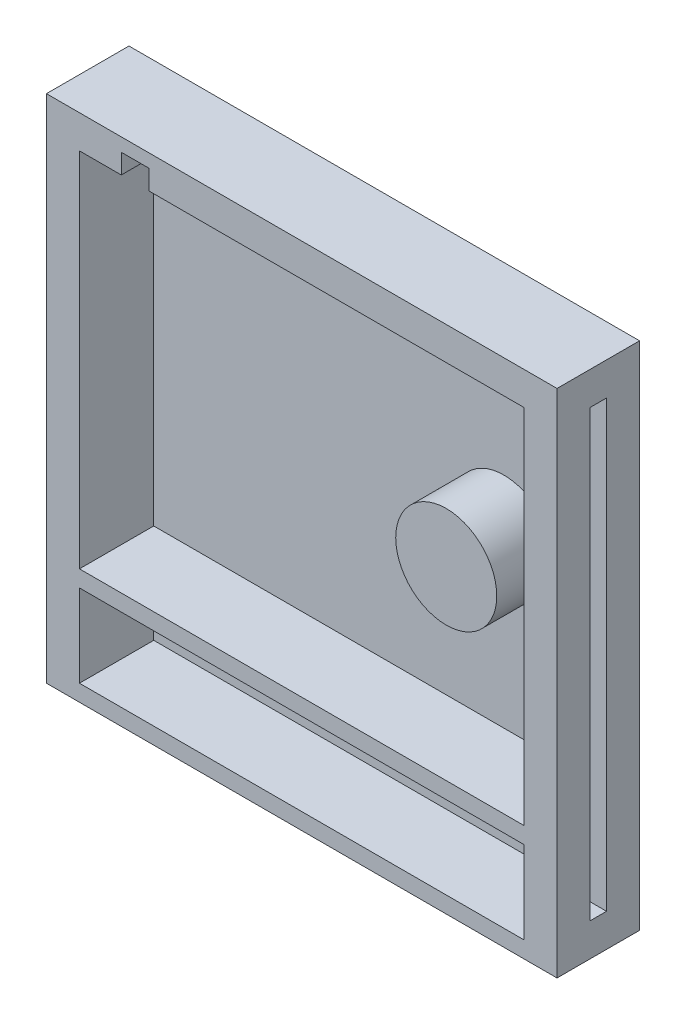
SolidWorks part; units mm, degrees
ref_plane "Front Plane" through (0, 0, 0) normal (0, 0, 1) x (1, 0, 0)
ref_plane "Top Plane" through (0, 0, 0) normal (0, 1, 0) x (1, 0, 0)
ref_plane "Right Plane" through (0, 0, 0) normal (1, 0, 0) x (0, 0, -1)
sketch "Sketch1" plane through (0, 0, 0) normal (0, 0, 1) x (1, 0, 0)
  line L1 (78.5679, 78.5679) -> (-78.5679, 78.5679)
  line L2 (78.5679, 78.5679) -> (78.5679, -78.5679)
  line L3 (78.5679, -78.5679) -> (-78.5679, -78.5679)
  line L4 (-78.5679, 78.5679) -> (-78.5679, -78.5679)
  line L5 (78.5679, 78.5679) -> (-78.5679, -78.5679) construction
  line L6 (78.5679, -78.5679) -> (-78.5679, 78.5679) construction
  point P0 (0, 0)
extrude "Boss-Extrude1" add sketch "Sketch1" along normal blind 25.4
sketch "Sketch2" plane through (0, 0, 25.4) normal (0, 0, 1) x (1, 0, 0)
  line L0 (78.5679, -78.5679) -> (78.5679, 78.5679) construction
  line L1 (68.4079, 68.4079) -> (-68.4079, 68.4079)
  line L2 (68.4079, 68.4079) -> (68.4079, -68.4079)
  line L3 (68.4079, -68.4079) -> (-68.4079, -68.4079)
  line L4 (-68.4079, 68.4079) -> (-68.4079, -68.4079)
  line L5 (68.4079, 68.4079) -> (-68.4079, -68.4079) construction
  line L6 (68.4079, -68.4079) -> (-68.4079, 68.4079) construction
  line L7 (-68.4079, -43.0079) -> (68.4079, -43.0079)
  point P0 (0, 0)
  dimension "D1" = 10.16
  dimension "D2" = 25.4
extrude "Cut-Extrude1" cut sketch "Sketch2" against normal offset from surface (22.86 mm away) 2.54 contours L4 L7 L2 L1 up to face at (0, 0, 0)
sketch "Sketch3" plane through (0, 0, 25.4) normal (0, 0, 1) x (1, 0, 0)
  line L0 (-68.4079, 68.4079) -> (-68.4079, -43.0079) construction
  line L1 (68.4079, -48.0879) -> (-68.4079, -48.0879)
  line L2 (68.4079, -48.0879) -> (68.4079, -73.4879)
  line L3 (68.4079, -73.4879) -> (-68.4079, -73.4879)
  line L4 (-68.4079, -48.0879) -> (-68.4079, -73.4879)
  line L5 (68.4079, 68.4079) -> (68.4079, -43.0079) construction
  line L6 (0, -48.0879) -> (0, -43.0079) construction
  line L7 (-68.4079, -43.0079) -> (68.4079, -43.0079) construction
  line L8 (0, -73.4879) -> (0, -78.5679) construction
  line L9 (-78.5679, -78.5679) -> (78.5679, -78.5679) construction
  dimension "D1" = 5.08
extrude "Cut-Extrude2" cut sketch "Sketch3" against normal offset from surface (22.86 mm away) 2.54 up to face at (0, 0, 0)
sketch "Sketch5" plane through (-78.5679, 0, 0) normal (-1, 0, 0) x (0, 0, 1)
  line L0 (15.24, 0) -> (25.4, 0) construction
  line L1 (15.24, -68.4079) -> (10.16, -68.4079)
  line L2 (15.24, -68.4079) -> (15.24, 68.4079)
  line L3 (15.24, 68.4079) -> (10.16, 68.4079)
  line L4 (10.16, -68.4079) -> (10.16, 68.4079)
  line L5 (25.4, 78.5679) -> (25.4, -78.5679) construction
  line L6 (10.16, 0) -> (0, 0) construction
  line L7 (0, 78.5679) -> (0, -78.5679) construction
  line L8 (25.4, 78.5679) -> (0, 78.5679) construction
  dimension "D1" = 5.08
  dimension "D2" = 10.16
extrude "Cut-Extrude3" cut sketch "Sketch5" against normal blind 7.62
mirror "Mirror1" about plane through (0, 0, 0) normal (1, 0, 0) of "Cut-Extrude3"
sketch "Sketch6" plane through (0, 0, 25.4) normal (0, 0, 1) x (1, 0, 0)
  line L0 (68.4079, 68.4079) -> (-68.4079, 68.4079) construction
  line L1 (-55.5371, 74.4708) -> (-47.0508, 74.4708)
  line L2 (-55.5371, 74.4708) -> (-55.5371, 68.4079)
  line L3 (-55.5371, 68.4079) -> (-47.0508, 68.4079)
  line L4 (-47.0508, 74.4708) -> (-47.0508, 68.4079)
extrude "Cut-Extrude4" cut sketch "Sketch6" against normal blind 15.24
sketch "Sketch7" plane through (0, 0, 2.54) normal (0, 0, 1) x (1, 0, 0)
  line L0 (39.7681, 29.7121) -> (39.7681, -10.9808) construction
  line L1 (53.9489, 29.7121) -> (53.9489, -10.9808)
  line L2 (25.5872, 29.7121) -> (25.5872, -10.9808)
  arc A0 (53.9489, 29.7121) -> (25.5872, 29.7121) centre (39.7681, 29.7121) ccw
  arc A1 (25.5872, -10.9808) -> (53.9489, -10.9808) centre (39.7681, -10.9808) ccw
  point P2 (39.7681, 9.3656)
extrude "Boss-Extrude2" [suppressed] add sketch "Sketch7" along normal blind 20.32
sketch "Sketch8" plane through (0, 0, 2.54) normal (0, 0, 1) x (1, 0, 0)
  circle A0 centre (39.3913, 8.8989) radius 15.5472
extrude "Boss-Extrude3" add sketch "Sketch8" along normal blind 17.78
